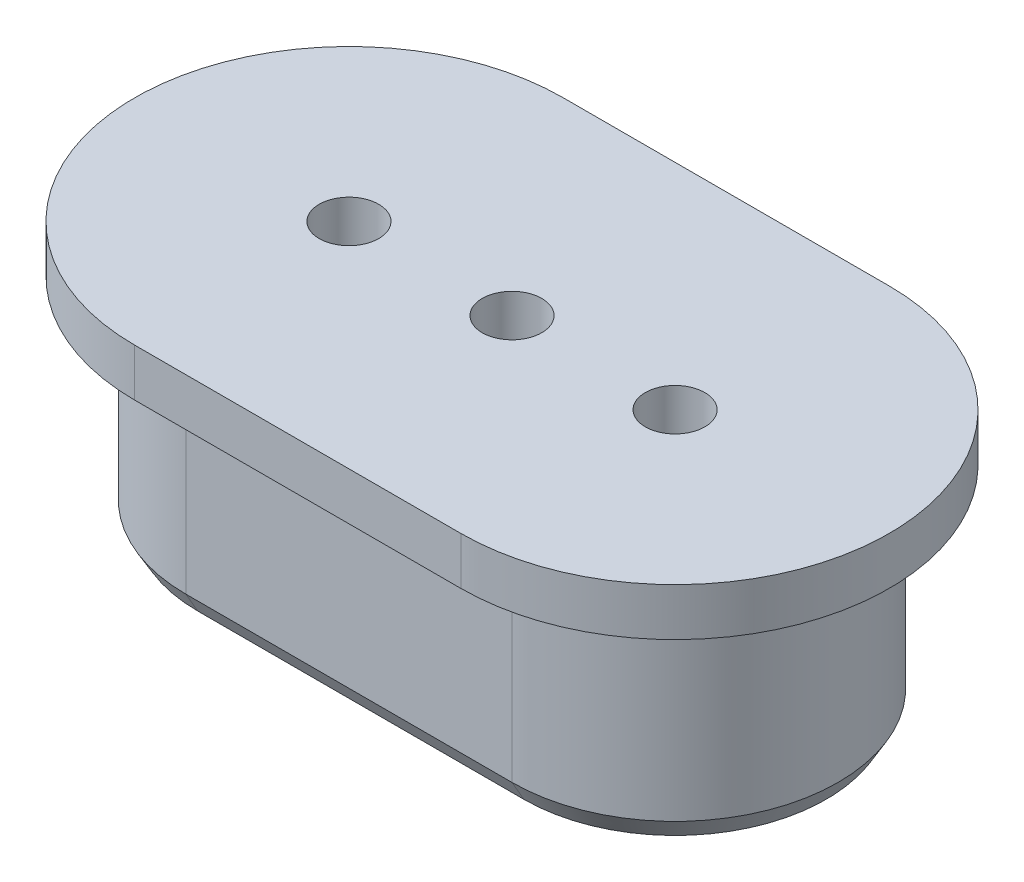
SolidWorks part; units mm, degrees
ref_plane "Front Plane" through (0, 0, 0) normal (0, 0, 1) x (1, 0, 0)
ref_plane "Top Plane" through (0, 0, 0) normal (0, 1, 0) x (1, 0, 0)
ref_plane "Right Plane" through (0, 0, 0) normal (1, 0, 0) x (0, 0, -1)
sketch "Sketch1" plane through (0, 0, 0) normal (0, 1, 0) x (1, 0, 0)
  line L0 (-3.425, 3.425) -> (3.425, 3.425)
  line L1 (-3.425, -3.425) -> (3.425, -3.425)
  line L2 (-3.425, 2.925) -> (3.425, 2.925)
  line L3 (-3.425, -2.925) -> (3.425, -2.925)
  circle A0 centre (3.425, 0) radius 3.425 construction
  circle A1 centre (-3.425, 0) radius 3.425 construction
  arc A2 (-3.425, 3.425) -> (-3.425, -3.425) centre (-3.425, 0) ccw
  arc A3 (3.425, 3.425) -> (3.425, -3.425) centre (3.425, 0) cw
  arc A4 (3.425, 2.925) -> (3.425, -2.925) centre (3.425, 0) cw
  arc A5 (-3.425, 2.925) -> (-3.425, -2.925) centre (-3.425, 0) ccw
  dimension "D1" = 6.85
  dimension "D2" = 6.85
  dimension "D3" = 0.5
extrude "Boss-Extrude1" add sketch "Sketch1" along normal blind 4.5
sketch "Sketch2" plane through (0, 4.5, 0) normal (0, 1, 0) x (1, 0, 0)
  line L0 (-3.425, 4.5) -> (3.425, 4.5)
  line L1 (-3.425, -4.5) -> (3.425, -4.5)
  arc A0 (-3.425, 4.5) -> (-3.425, -4.5) centre (-3.425, 0) ccw
  arc A1 (3.425, 4.5) -> (3.425, -4.5) centre (3.425, 0) cw
  arc A2 (-3.425, 3.425) -> (-3.425, -3.425) centre (-3.425, 0) ccw construction
  arc A3 (3.425, -3.425) -> (3.425, 3.425) centre (3.425, 0) ccw construction
  circle A4 centre (-3.425, 0) radius 0.625
  circle A5 centre (3.425, 0) radius 0.625
  dimension "D1" = 1.25
  dimension "D2" = 4.5
extrude "Boss-Extrude2" add sketch "Sketch2" along normal blind 1
chamfer "Chamfer2" distance 0.25 angle 60 4 edges at (-6.85, 0, 0) (0, 0, 3.425) (6.85, 0, 0) (0, 0, -3.425)
sketch "Sketch3" plane through (0, 5.5, 0) normal (0, 1, 0) x (1, 0, 0)
  circle A0 centre (0, 0) radius 0.625
  circle A1 centre (3.425, 0) radius 0.625 construction
extrude "Cut-Extrude1" cut sketch "Sketch3" against normal through all both and the other way through all
equation "\"0.5mmmm\"=1"
